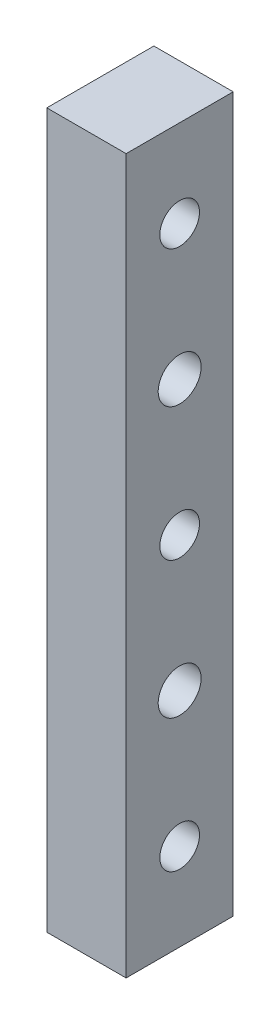
SolidWorks part; units mm, degrees
ref_plane "Front Plane" through (0, 0, 0) normal (0, 0, 1) x (1, 0, 0)
ref_plane "Top Plane" through (0, 0, 0) normal (0, 1, 0) x (1, 0, 0)
ref_plane "Right Plane" through (0, 0, 0) normal (1, 0, 0) x (0, 0, -1)
sketch "Sketch1" plane through (0, 0, 0) normal (1, 0, 0) x (0, 0, -1)
  line L1 (-4.7849, 53.6278) -> (8.7151, 53.6278)
  line L2 (-4.7849, 53.6278) -> (-4.7849, -36.3722)
  line L3 (-4.7849, -36.3722) -> (8.7151, -36.3722)
  line L4 (8.7151, 53.6278) -> (8.7151, -36.3722)
  dimension "D1" = 90
  dimension "D2" = 13.5
extrude "Boss-Extrude1" add sketch "Sketch1" along normal blind 10
hole_wizard "1/4-28 Tapped Hole1" positions "Sketch3" profile "Sketch2" tap size "1/4-28" standard "Ansi Inch" end condition through all
sketch "Sketch3" plane through (10, 0, 0) normal (1, 0, 0) x (0, 0, -1)
  line L0 (1.9651, 53.6278) -> (1.9651, -36.3722) construction
  line L1 (8.7151, 53.6278) -> (-4.7849, 53.6278) construction
  line L2 (-4.7849, -36.3722) -> (8.7151, -36.3722) construction
  line L3 (-4.7849, 53.6278) -> (-4.7849, -36.3722) construction
  point P0 (1.9651, 25.6278)
  point P1 (1.9651, -8.3722)
  point P8 (-4.7849, 8.6278)
  dimension "D1" = 17
  dimension "D2" = 34
sketch "Sketch2" plane through (10, 25.6278, -1.9651) normal (0, 1, 0) x (0, 0, -1)
  line L0 (0, 0) -> (0, 10)
  line L1 (0, 10) -> (2.7051, 10)
  line L2 (2.7051, 10) -> (2.7051, 0)
  line L5 (2.7051, 0) -> (0, 0)
  line L11 (0, -6.35) -> (0, 107.95) construction
  dimension "Thru Tap Drill Dia." = 5.4102
  dimension "Thru Tap Drill Depth" = 10
cosmetic thread "Hole Thread1" parameters "D1"=10, "D2"=6.35
cosmetic thread "Hole Thread2" parameters "D1"=10, "D2"=6.35
hole_wizard "Ø5.0 (5) Diameter Hole1" positions "Sketch5" profile "Sketch4" hole size "Ø5.0" standard "Ansi Metric"
sketch "Sketch5" plane through (10, 0, 0) normal (1, 0, 0) x (0, 0, -1)
  line L0 (1.9651, 53.6278) -> (1.9651, -36.3722) construction
  line L1 (8.7151, 53.6278) -> (-4.7849, 53.6278) construction
  line L2 (-4.7849, -36.3722) -> (8.7151, -36.3722) construction
  line L5 (1.9651, 42.6278) -> (1.9651, -25.3722) construction
  circle A0 centre (1.9651, 25.6278) radius 2.7051 construction
  circle A1 centre (1.9651, -8.3722) radius 2.7051 construction
  point P0 (1.9651, 42.6278)
  point P1 (1.9651, -25.3722)
  point P27 (1.9651, 8.6278)
  dimension "D1" = 17
  dimension "D2" = 17
sketch "Sketch4" plane through (10, 42.6278, -1.9651) normal (0, 1, 0) x (0, 0, -1)
  line L0 (0, 0) -> (0, 51.0022)
  line L1 (0, 51.0022) -> (2.5, 49.5)
  line L2 (2.5, 49.5) -> (2.5, 0)
  line L5 (2.5, 0) -> (0, 0)
  line L10 (0, 51.0022) -> (-2.5, 49.5) construction
  line L11 (0, -6.35) -> (0, 107.95) construction
  dimension "Hole Dia." = 5
  dimension "Hole Depth" = 49.5
  dimension "Drill Angle" = 118
sketch "Sketch6" plane through (10, 0, 0) normal (1, 0, 0) x (0, 0, -1)
  line L0 (1.9651, 33.1278) -> (1.9651, 18.1278) construction
  line L1 (5.0651, 33.1278) -> (5.0651, 18.1278)
  line L2 (-1.1349, 33.1278) -> (-1.1349, 18.1278)
  line L3 (1.9651, -0.8722) -> (1.9651, -15.8722) construction
  line L4 (5.0651, -0.8722) -> (5.0651, -15.8722)
  line L5 (-1.1349, -0.8722) -> (-1.1349, -15.8722)
  line L6 (1.9651, 33.1278) -> (1.9651, 18.1278) construction
  line L7 (6.8651, 33.1278) -> (6.8651, 18.1278)
  line L8 (-2.9349, 33.1278) -> (-2.9349, 18.1278)
  line L9 (1.9651, -0.8722) -> (1.9651, -15.8722) construction
  line L10 (6.8651, -0.8722) -> (6.8651, -15.8722)
  line L11 (-2.9349, -0.8722) -> (-2.9349, -15.8722)
  arc A0 (5.0651, 33.1278) -> (-1.1349, 33.1278) centre (1.9651, 33.1278) ccw
  arc A1 (-1.1349, 18.1278) -> (5.0651, 18.1278) centre (1.9651, 18.1278) ccw
  arc A2 (5.0651, -0.8722) -> (-1.1349, -0.8722) centre (1.9651, -0.8722) ccw
  arc A3 (-1.1349, -15.8722) -> (5.0651, -15.8722) centre (1.9651, -15.8722) ccw
  arc A4 (6.8651, 33.1278) -> (-2.9349, 33.1278) centre (1.9651, 33.1278) ccw
  arc A5 (-2.9349, 18.1278) -> (6.8651, 18.1278) centre (1.9651, 18.1278) ccw
  arc A6 (6.8651, -0.8722) -> (-2.9349, -0.8722) centre (1.9651, -0.8722) ccw
  arc A7 (-2.9349, -15.8722) -> (6.8651, -15.8722) centre (1.9651, -15.8722) ccw
  point P2 (1.9651, 25.6278)
  point P7 (1.9651, -8.3722)
  point P18 (1.9651, 25.6278)
  point P23 (1.9651, -8.3722)
  dimension "D1" = 6.2
  dimension "D2" = 15
  dimension "D3" = 1.8
  dimension "D4" = 15
extrude "Cut-Extrude1" [suppressed] cut sketch "Sketch6" against normal blind 1
sketch "Sketch7" plane through (0, 0, 0) normal (-1, 0, 0) x (0, 0, 1)
  line L1 (2.0099, 40.3329) -> (2.0099, 44.9228)
  line L2 (2.0099, 44.9228) -> (-1.9651, 47.2178)
  line L3 (-1.9651, 47.2178) -> (-5.9401, 44.9228)
  line L4 (-5.9401, 44.9228) -> (-5.9401, 40.3329)
  line L5 (-5.9401, 40.3329) -> (-1.9651, 38.0379)
  line L6 (-1.9651, 38.0379) -> (2.0099, 40.3329)
  line L7 (2.0099, 6.3329) -> (2.0099, 10.9228)
  line L8 (2.0099, 10.9228) -> (-1.9651, 13.2178)
  line L9 (-1.9651, 13.2178) -> (-5.9401, 10.9228)
  line L10 (-5.9401, 10.9228) -> (-5.9401, 6.3329)
  line L11 (-5.9401, 6.3329) -> (-1.9651, 4.0379)
  line L12 (-1.9651, 4.0379) -> (2.0099, 6.3329)
  line L13 (2.0099, -27.6671) -> (2.0099, -23.0772)
  line L14 (2.0099, -23.0772) -> (-1.9651, -20.7822)
  line L15 (-1.9651, -20.7822) -> (-5.9401, -23.0772)
  line L16 (-5.9401, -23.0772) -> (-5.9401, -27.6671)
  line L17 (-5.9401, -27.6671) -> (-1.9651, -29.9621)
  line L18 (-1.9651, -29.9621) -> (2.0099, -27.6671)
  circle A0 centre (-1.9651, 42.6278) radius 3.975 construction
  circle A1 centre (-1.9651, 8.6278) radius 3.975 construction
  circle A2 centre (-1.9651, -25.3722) radius 3.975 construction
  dimension "D1" = 7.95
extrude "Cut-Extrude2" cut sketch "Sketch7" against normal blind 5
